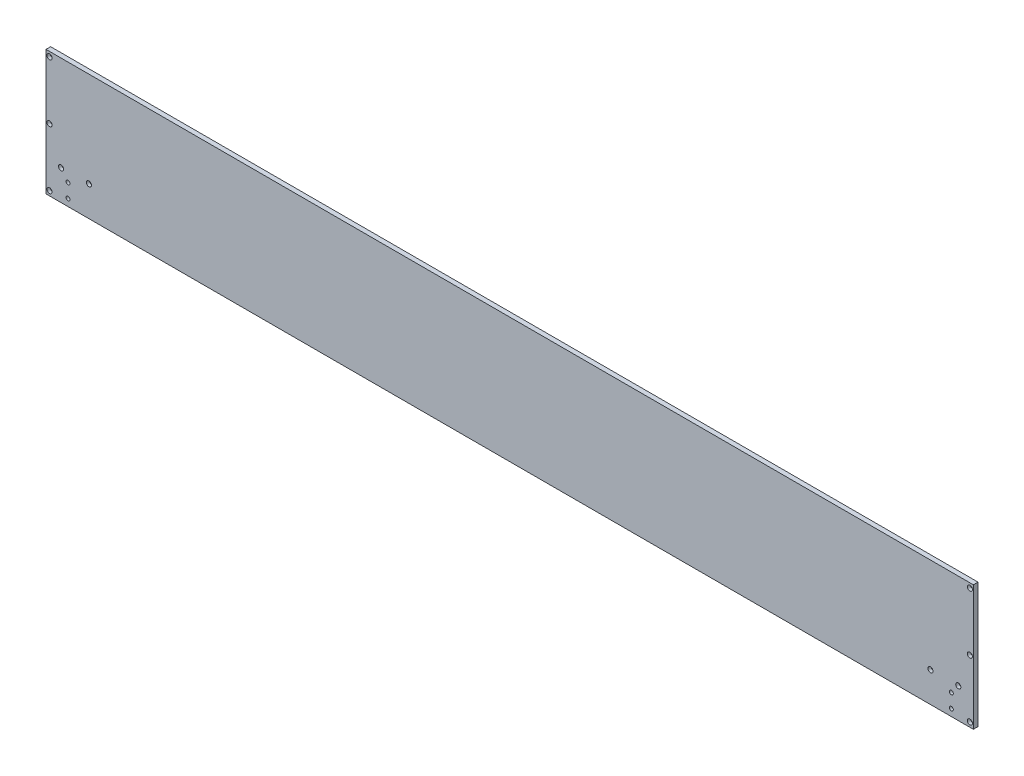
SolidWorks part; units mm, degrees
material "A3钢"
ref_plane "前视基准面" through (0, 0, 0) normal (0, 0, 1) x (1, 0, 0)
ref_plane "上视基准面" through (0, 0, 0) normal (0, 1, 0) x (1, 0, 0)
ref_plane "右视基准面" through (0, 0, 0) normal (1, 0, 0) x (0, 0, -1)
sketch "草图1" plane through (0, 0, 0) normal (0, 0, 1) x (1, 0, 0)
  line L1 (-1000, -135) -> (1000, -135)
  line L2 (-1000, -135) -> (-1000, 135)
  line L3 (-1000, 135) -> (1000, 135)
  line L4 (1000, -135) -> (1000, 135)
  line L5 (-1000, -135) -> (1000, 135) construction
  line L6 (-1000, 135) -> (1000, -135) construction
  point P0 (0, 0)
  dimension "D1" = 2000
  dimension "D2" = 270
extrude "凸台-拉伸1" add sketch "草图1" along normal mid plane 10
sketch "草图2" plane through (0, 0, 5) normal (0, 0, 1) x (1, 0, 0)
  line L0 (0, 619.8775) -> (0, -680.849) construction
  line L1 (-1000, 135) -> (-1000, -135) construction
  line L2 (-992.5, -125) -> (992.5, -125)
  line L3 (-992.5, -125) -> (-992.5, 125)
  line L4 (-992.5, 125) -> (992.5, 125)
  line L5 (992.5, -125) -> (992.5, 125)
  line L6 (-992.5, -125) -> (992.5, 125) construction
  line L7 (-992.5, 125) -> (992.5, -125) construction
  line L8 (-992.5, 0) -> (1266.3795, 0) construction
  point P3 (0, 0)
  dimension "D1" = 7.5
  dimension "D2" = 250
hole_wizard "打孔尺寸(%根据)内六角圆柱头螺钉的类型1" positions "3D草图1" profile "草图3" counterbore size "M6" standard "GB" end condition through all
sketch3d "3D草图1"
  line L0 (992.5, -125, 5) -> (992.5, 125, 5) construction
  point P0 (-992.5, 125, 5)
  point P3 (-992.5, -125, 5)
  point P6 (992.5, 125, 5)
  point P9 (992.5, -125, 5)
  point P12 (992.5, 0, 5)
  point P14 (-992.5, 0, 5)
sketch "草图3" plane through (-992.5, 125, 5) normal (1, 0, 0) x (0, -1, 0)
  line L0 (0, 0) -> (0, 10)
  line L1 (0, 10) -> (3.3, 10)
  line L3 (3.3, 10) -> (3.3, 6.8)
  line L4 (3.3, 6.8) -> (5.5, 6.8)
  line L5 (5.5, 6.8) -> (5.5, 0)
  line L7 (5.5, 0) -> (0, 0)
  line L11 (0, -6.35) -> (0, 107.95) construction
  dimension "通孔孔直径" = 6.6
  dimension "通孔孔深度" = 10
  dimension "柱形沉头孔直径" = 11
  dimension "柱形沉头孔深度" = 6.8
sketch "草图4" plane through (0, 0, 5) normal (0, 0, 1) x (1, 0, 0)
  line L0 (-660, -70) -> (-330, -70) construction
  line L1 (-330, -70) -> (330, -70) construction
  line L2 (330, -70) -> (660, -70) construction
  line L4 (-1000, -135) -> (1000, -135) construction
  line L5 (0, -500.4396) -> (0, 557.8999) construction
  dimension "D1" = 65
  dimension "D2" = 660
  dimension "D3" = 330
sketch "草图7" plane through (0, 0, 5) normal (0, 0, 1) x (1, 0, 0)
  line L0 (1000, -135) -> (1000, 135) construction
  line L1 (-1000, -135) -> (1000, -135) construction
  circle A0 centre (927.5, -105) radius 4
  dimension "D1" = 72.5
  dimension "D2" = 30
  dimension "D3" = 8
sketch "草图10" plane through (0, 0, 5) normal (0, 0, 1) x (1, 0, 0)
  line L0 (-1000, -70) -> (-967.5, -70) construction
  line L1 (-967.5, -70) -> (-907.5, -70) construction
  line L3 (-1000, 135) -> (-1000, -135) construction
  line L4 (-1000, -135) -> (1000, -135) construction
  dimension "D1" = 60
  dimension "D2" = 32.5
  dimension "D3" = 65
sketch "草图13" plane through (0, 0, -5) normal (0, 0, -1) x (-1, 0, 0)
  line L0 (0, 239.8087) -> (0, -409.6798) construction
  line L1 (1000, -135) -> (-1000, -135) construction
  line L2 (-255, -118) -> (255, -118)
  line L3 (-255, -118) -> (-255, -88)
  line L4 (-255, -88) -> (255, -88)
  line L5 (255, -118) -> (255, -88)
  line L6 (-255, -118) -> (255, -88) construction
  line L7 (-255, -88) -> (255, -118) construction
  point P3 (0, -103)
  dimension "D1" = 510
  dimension "D2" = 30
  dimension "D3" = 17
sketch "草图15" plane through (0, 0, -5) normal (0, 0, -1) x (-1, 0, 0)
  line L0 (-350, 162) -> (-350, -87.2009) construction
  line L1 (0, 0) -> (0, 219.6539) construction
  line L3 (-378.25, 67.25) -> (-321.75, 67.25)
  line L4 (1000, -135) -> (-1000, -135) construction
  line L5 (-400, 9) -> (-300, 9)
  line L6 (-400, 9) -> (-400, 69)
  line L7 (-400, 69) -> (-300, 69)
  line L8 (-300, 9) -> (-300, 69)
  line L9 (-400, 9) -> (-300, 69) construction
  line L10 (-400, 69) -> (-300, 9) construction
  line L11 (-378.25, 67.25) -> (-378.25, 10.75)
  line L12 (-378.25, 10.75) -> (-321.75, 10.75)
  line L13 (-321.75, 67.25) -> (-321.75, 10.75)
  line L14 (-378.25, 67.25) -> (-321.75, 10.75) construction
  line L15 (-378.25, 10.75) -> (-321.75, 67.25) construction
  point P6 (-350, 39)
  point P11 (-350, 39)
  dimension "D1" = 100
  dimension "D2" = 60
  dimension "D3" = 144
  dimension "D4" = 350
  dimension "D5" = 56.5
sketch "草图17" plane through (0, 0, -5) normal (0, 0, -1) x (-1, 0, 0)
  line L0 (0, 0) -> (0, 418.4231) construction
  line L2 (-45, -53) -> (45, -53)
  line L3 (-45, -53) -> (-45, 7)
  line L4 (-45, 7) -> (45, 7)
  line L5 (45, -53) -> (45, 7)
  line L6 (-45, -53) -> (45, 7) construction
  line L7 (-45, 7) -> (45, -53) construction
  line L8 (1000, -135) -> (-1000, -135) construction
  point P3 (0, -23)
  dimension "D1" = 112
  dimension "D2" = 90
  dimension "D3" = 60
sketch "草图18" plane through (0, 0, 5) normal (0, 0, 1) x (1, 0, 0)
  line L0 (-952.5, -90) -> (-952.5, -120) construction
  line L1 (-1000, -135) -> (1000, -135) construction
  line L2 (-1000, 135) -> (-1000, -135) construction
  dimension "D1" = 30
  dimension "D2" = 15
  dimension "D3" = 47.5
hole_wizard "M10 螺纹孔1" positions "3D草图2" profile "草图19" tap size "M10" standard "GB" end condition through all
sketch3d "3D草图2"
  point P0 (-952.5, -90, 5)
  point P3 (-952.5, -120, 5)
sketch "草图19" plane through (-952.5, -90, 5) normal (1, 0, 0) x (0, -1, 0)
  line L0 (0, 0) -> (0, 10)
  line L1 (0, 10) -> (4.25, 10)
  line L2 (4.25, 10) -> (4.25, 0)
  line L5 (4.25, 0) -> (0, 0)
  line L11 (0, -6.35) -> (0, 107.95) construction
  dimension "通孔螺纹孔钻头直径" = 8.5
  dimension "通孔螺纹孔钻头深度" = 10
cosmetic thread "孔螺蚊线3" parameters "D2"=10
cosmetic thread "孔螺蚊线4" parameters "D2"=10
mirror "镜向1" about plane through (0, 0, 0) normal (1, 0, 0) of "M10 螺纹孔1"
sketch "草图20" plane through (0, 0, 5) normal (0, 0, 1) x (1, 0, 0)
  line L0 (907.5, -70) -> (967.5, -70) construction
  line L1 (1000, -135) -> (1000, 135) construction
  line L2 (-1000, -135) -> (1000, -135) construction
  dimension "D1" = 60
  dimension "D2" = 32.5
  dimension "D3" = 65
hole_wizard "打孔尺寸(%根据)内六角圆柱头螺钉的类型2" positions "3D草图3" profile "草图22" counterbore size "M6" standard "GB" end condition through all
sketch3d "3D草图3"
  point P0 (907.5, -70, 5)
  point P3 (967.5, -70, 5)
sketch "草图22" plane through (907.5, -70, 5) normal (1, 0, 0) x (0, -1, 0)
  line L0 (0, 0) -> (0, 10)
  line L1 (0, 10) -> (3.3, 10)
  line L3 (3.3, 10) -> (3.3, 6.8)
  line L4 (3.3, 6.8) -> (5.5, 6.8)
  line L5 (5.5, 6.8) -> (5.5, 0)
  line L7 (5.5, 0) -> (0, 0)
  line L11 (0, -6.35) -> (0, 107.95) construction
  dimension "通孔孔直径" = 6.6
  dimension "通孔孔深度" = 10
  dimension "柱形沉头孔直径" = 11
  dimension "柱形沉头孔深度" = 6.8
mirror "镜向2" about plane through (0, 0, 0) normal (1, 0, 0) of "打孔尺寸(%根据)内六角圆柱头螺钉的类型2"
